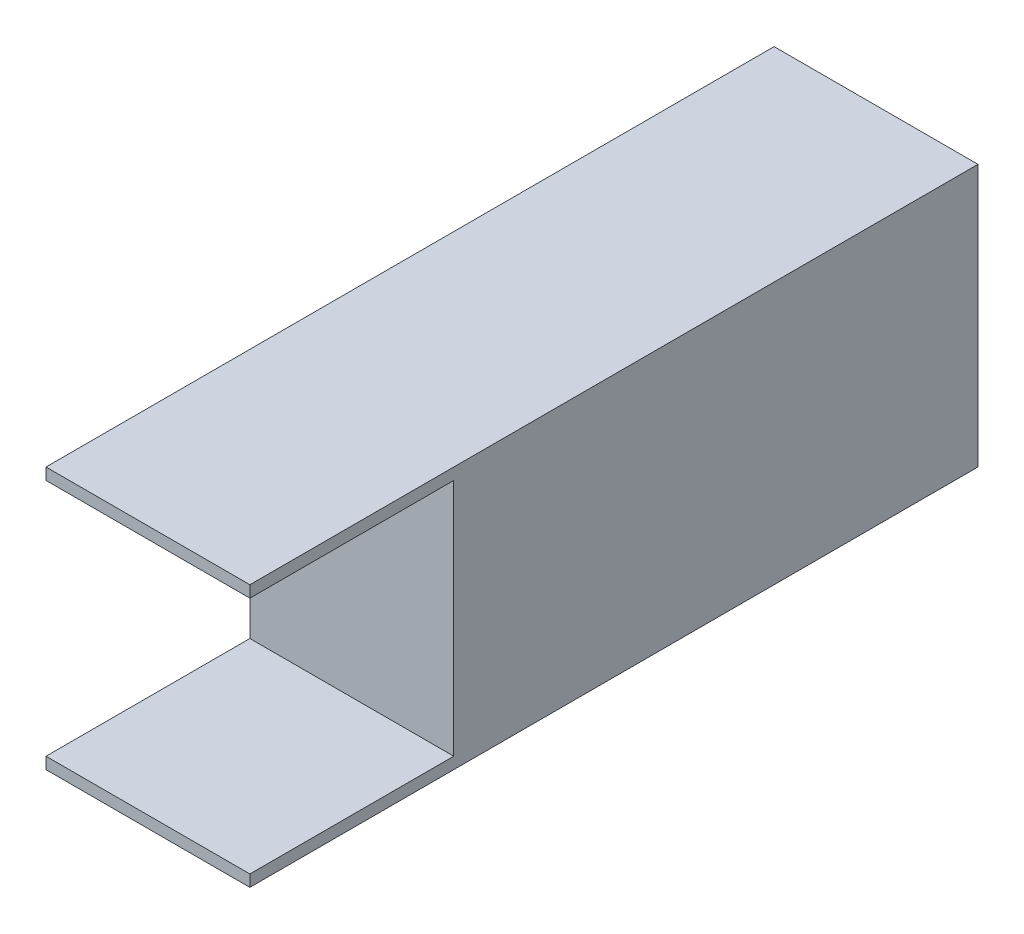
SolidWorks part; units mm, degrees
material "6063-T5"
ref_plane "Front Plane" through (0, 0, 0) normal (0, 0, 1) x (1, 0, 0)
ref_plane "Top Plane" through (0, 0, 0) normal (0, 1, 0) x (1, 0, 0)
ref_plane "Right Plane" through (0, 0, 0) normal (1, 0, 0) x (0, 0, -1)
sketch "Sketch1" plane through (0, 0, 0) normal (0, 0, 1) x (1, 0, 0)
  line L1 (-17.5, -22.5) -> (17.5, -22.5)
  line L2 (-17.5, -22.5) -> (-17.5, 22.5)
  line L3 (-17.5, 22.5) -> (17.5, 22.5)
  line L4 (17.5, -22.5) -> (17.5, 22.5)
  line L5 (-17.5, -22.5) -> (17.5, 22.5) construction
  line L6 (-17.5, 22.5) -> (17.5, -22.5) construction
  point P0 (0, 0)
  dimension "D1" = 35
  dimension "D2" = 45
extrude "Boss-Extrude1" add sketch "Sketch1" along normal blind 125
sketch "Sketch2" plane through (-17.5, 0, 0) normal (-1, 0, 0) x (0, 0, 1)
  line L1 (125, 20.5) -> (90, 20.5)
  line L2 (125, 20.5) -> (125, -20.5)
  line L3 (125, -20.5) -> (90, -20.5)
  line L4 (90, 20.5) -> (90, -20.5)
  line L5 (125, 22.5) -> (0, 22.5) construction
  line L6 (125, -22.5) -> (0, -22.5) construction
  line L7 (125, 22.5) -> (125, -22.5) construction
  dimension "D1" = 35
  dimension "D3" = 2
  dimension "D4" = 2
extrude "Cut-Extrude1" cut sketch "Sketch2" against normal through all
